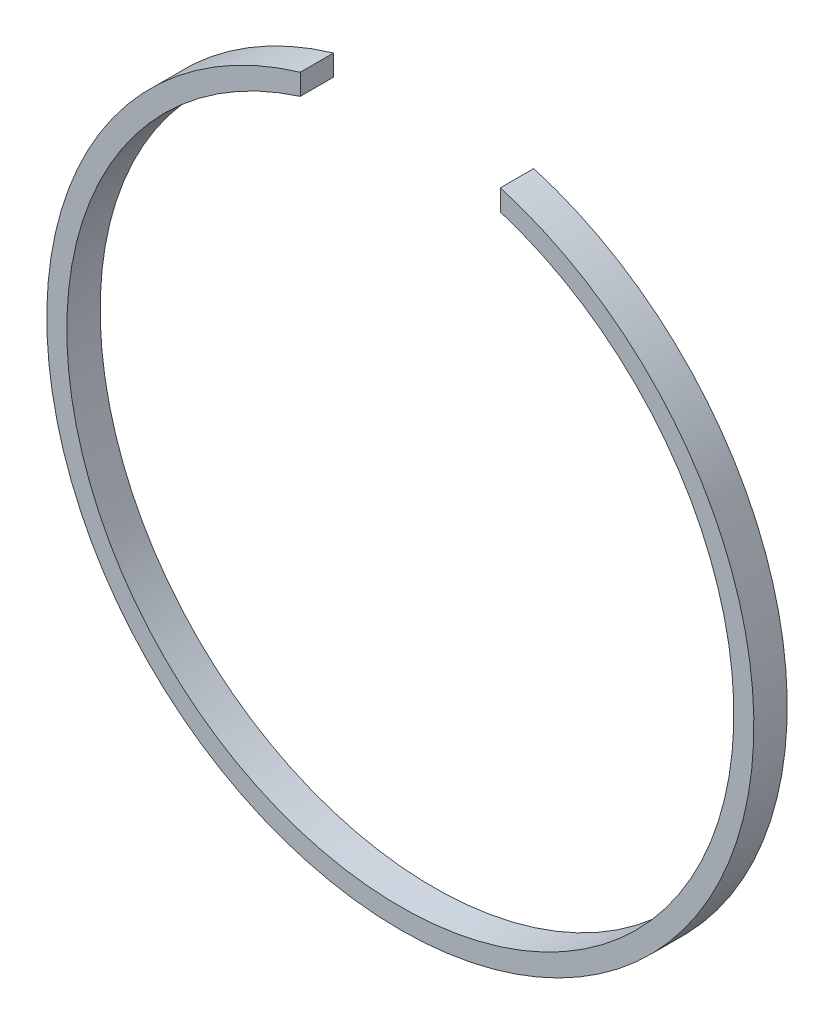
SolidWorks part; units mm, degrees
ref_plane "前视基准面" through (0, 0, 0) normal (0, 0, 1) x (1, 0, 0)
ref_plane "上视基准面" through (0, 0, 0) normal (0, 1, 0) x (1, 0, 0)
ref_plane "右视基准面" through (0, 0, 0) normal (1, 0, 0) x (0, 0, -1)
sketch "草图1" plane through (0, 0, 0) normal (0, 0, 1) x (1, 0, 0)
  circle A0 centre (0, 0) radius 50
  dimension "D1" = 100
extrude "拉伸-薄壁1" add sketch "草图1" along normal blind 5 thin
sketch "草图2" plane through (0, 0, 5) normal (0, 0, 1) x (1, 0, 0)
  line L1 (-15, 65) -> (15, 65)
  line L2 (-15, 65) -> (-15, 35)
  line L3 (-15, 35) -> (15, 35)
  line L4 (15, 65) -> (15, 35)
  line L5 (-15, 65) -> (15, 35) construction
  line L6 (-15, 35) -> (15, 65) construction
  point P4 (0, 50)
  point P5 (0, 0)
  dimension "D1" = 30
  dimension "D2" = 30
  dimension "D3" = 50
extrude "切除-拉伸1" cut sketch "草图2" against normal blind 10
